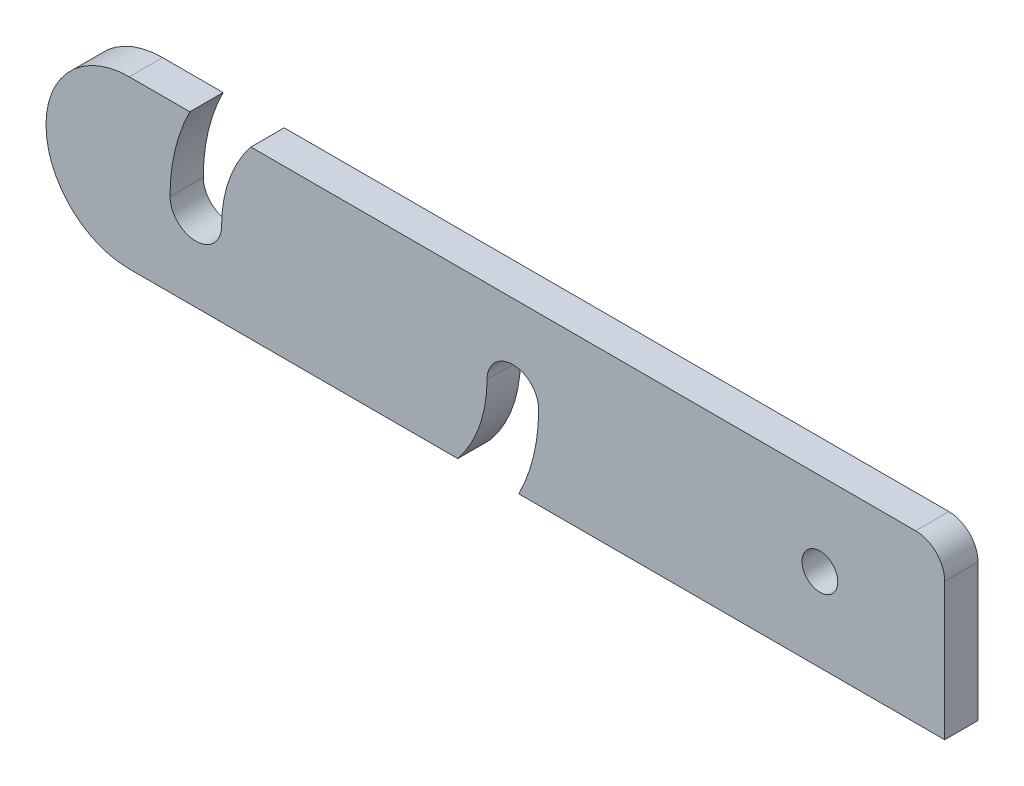
SolidWorks part; units mm, degrees
ref_plane "Front Plane" through (0, 0, 0) normal (0, 0, 1) x (1, 0, 0)
ref_plane "Top Plane" through (0, 0, 0) normal (0, 1, 0) x (1, 0, 0)
ref_plane "Right Plane" through (0, 0, 0) normal (1, 0, 0) x (0, 0, -1)
sketch "Sketch1" plane through (0, 0, 0) normal (0, 0, 1) x (1, 0, 0)
  line L2 (20.7866, -13) -> (-18.695, -13)
  line L5 (28.1245, -13) -> (79.305, -13)
  line L6 (-4.0716, 7) -> (75.805, 7)
  line L7 (79.305, -13) -> (79.305, 3.5)
  line L8 (30.51, -3) -> (64.305, -3) construction
  line L9 (-10.695, -3) -> (27.41, -3) construction
  line L10 (-18.695, 7) -> (-11.4095, 7)
  arc A0 (-13.795, -3) -> (-7.595, -3) centre (-10.695, -3) ccw
  arc A1 (30.51, -3) -> (24.31, -3) centre (27.41, -3) ccw
  circle A2 centre (64.305, -3) radius 2.15
  arc A3 (-18.695, -13) -> (-18.695, 7) centre (-18.695, -3) cw
  arc A4 (-4.0716, 7) -> (-7.595, -3) centre (8.3575, -3) ccw
  arc A5 (28.1245, -13) -> (30.51, -3) centre (8.3575, -3) ccw
  arc A6 (20.7866, -13) -> (24.31, -3) centre (8.3575, -3) ccw
  arc A7 (-11.4095, 7) -> (-13.795, -3) centre (8.3575, -3) ccw
  arc A8 (79.305, 3.5) -> (75.805, 7) centre (75.805, 3.5) ccw
  dimension "D1" = 3.1
  dimension "D2" = 4.3
  dimension "D5" = 90
  dimension "D6" = 3.5
  dimension "D3" = 38.105
  dimension "D4" = 8
  dimension "D9" = 75
extrude "Boss-Extrude1" add sketch "Sketch1" along normal blind 4
